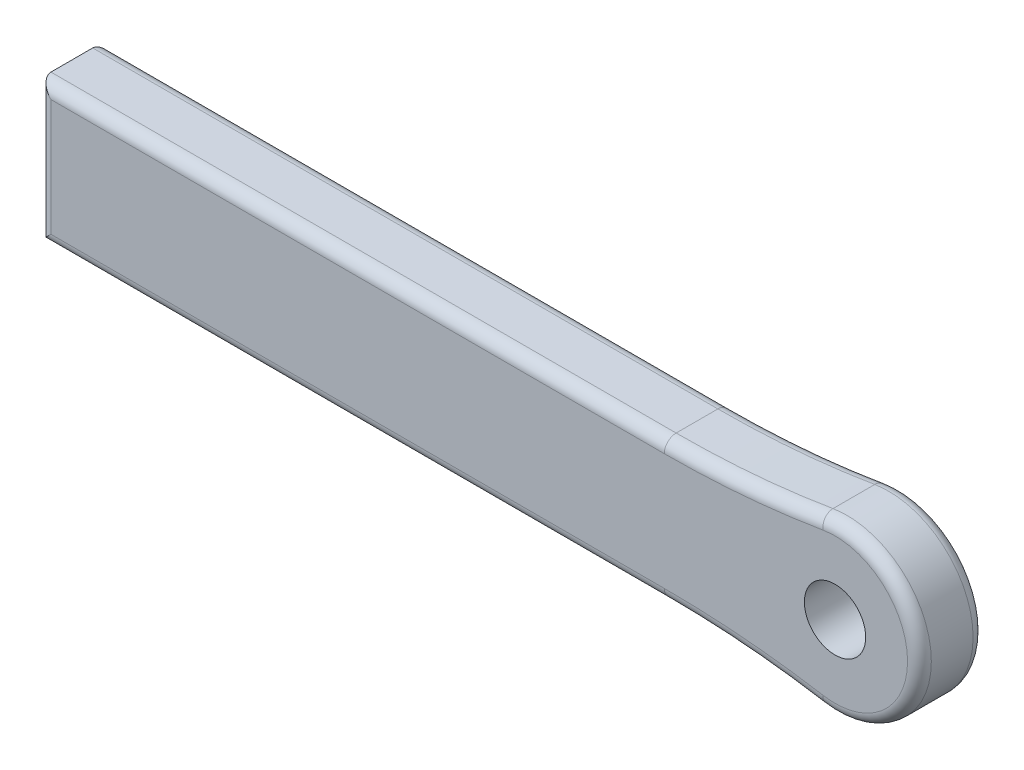
SolidWorks part; units mm, degrees
ref_plane "Front Plane" through (0, 0, 0) normal (0, 0, 1) x (1, 0, 0)
ref_plane "Top Plane" through (0, 0, 0) normal (0, 1, 0) x (1, 0, 0)
ref_plane "Right Plane" through (0, 0, 0) normal (1, 0, 0) x (0, 0, -1)
sketch "Sketch1" plane through (0, 0, 0) normal (0, 0, 1) x (1, 0, 0)
  line L1 (-80, -15) -> (53.5243, -15)
  line L2 (-80, -15) -> (-80, 15)
  line L3 (-80, 15) -> (53.5243, 15)
  line L5 (-80, -15) -> (80, 15) construction
  line L6 (-80, 15) -> (80, -15) construction
  arc A0 (87.0276, -17.781) -> (87.0276, 17.781) centre (90, 0) ccw
  arc A1 (53.5243, 15) -> (87.0276, 17.781) centre (53.5243, 218.2) ccw
  arc A2 (53.5243, -15) -> (87.0276, -17.781) centre (53.5243, -218.2) cw
  point P0 (0, 0)
  point P7 (0, 0)
  point P8 (-80, 0)
  dimension "D2" = 160
  dimension "D3" = 30
  dimension "D4" = 203.2
  dimension "D1" = 170
extrude "Boss-Extrude1" add sketch "Sketch1" along normal blind 14
fillet "Fillet1" radius 2.54 6 edges at (-13.2379, 15, 14) (70.3335, 15.6964, 14) (108.0278, 0, 14) (70.3335, -15.6964, 14) (-13.2379, -15, 14) (-80, 0, 14)
fillet "Fillet2" radius 2.54 6 edges at (-13.2379, -15, 0) (70.3335, -15.6964, 0) (108.0278, 0, 0) (70.3335, 15.6964, 0) (-13.2379, 15, 0) (-80, 0, 0)
hole_wizard "9/16-18 Tapped Hole1" positions "Sketch3" profile "Sketch4" tap size "9/16-18" standard "ANSI Inch" end condition through all
sketch "Sketch3" plane through (0, 0, 14) normal (0, 0, 1) x (1, 0, 0)
  line L0 (-80, -15) -> (-80, 15) construction
  point P0 (90, 0)
  dimension "D1" = 170
sketch "Sketch4" plane through (90, 0, 14) normal (1, 0, 0) x (0, -1, 0)
  line L0 (0, 0) -> (0, 14)
  line L1 (0, 14) -> (6.5481, 14)
  line L2 (6.5481, 14) -> (6.5481, 0)
  line L5 (6.5481, 0) -> (0, 0)
  line L11 (0, -6.35) -> (0, 107.95) construction
  dimension "Thru Tap Drill Dia." = 13.0962
  dimension "Thru Tap Drill Depth" = 14
cosmetic thread "Hole Thread1" parameters "D2"=14.2875
